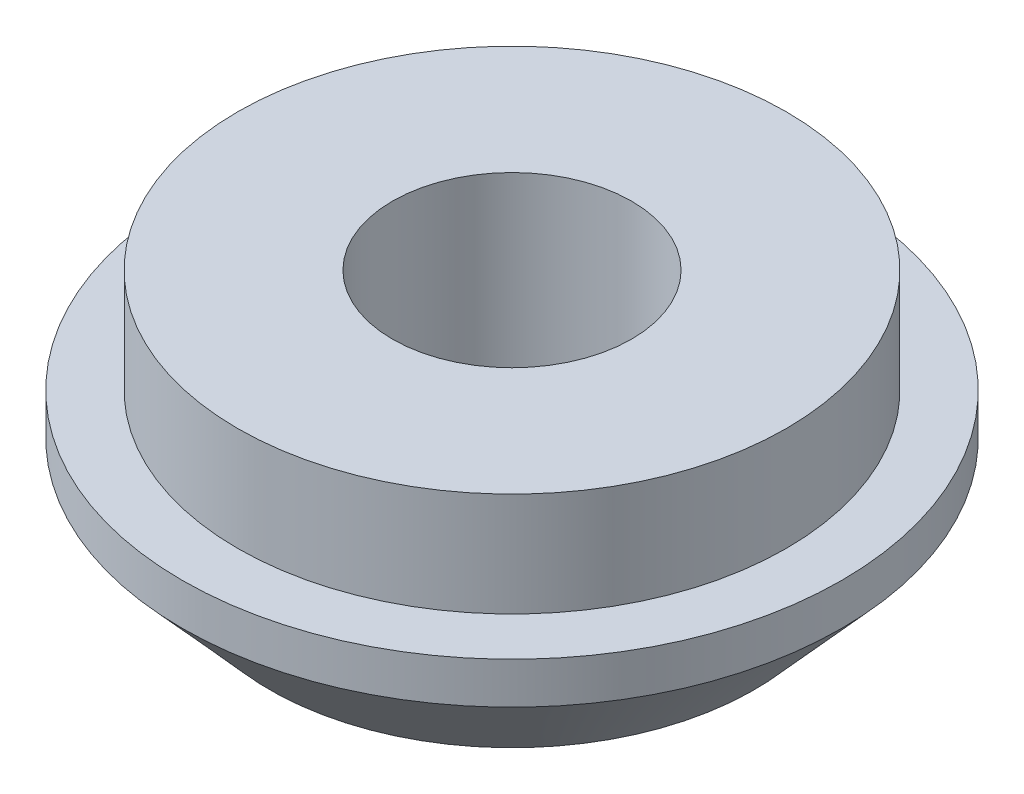
SolidWorks part; units mm, degrees
material "Plain Carbon Steel"
ref_plane "Front Plane" through (0, 0, 0) normal (0, 0, 1) x (1, 0, 0)
ref_plane "Top Plane" through (0, 0, 0) normal (0, 1, 0) x (1, 0, 0)
ref_plane "Right Plane" through (0, 0, 0) normal (1, 0, 0) x (0, 0, -1)
sketch "Sketch1" plane through (0, 0, 0) normal (0, 1, 0) x (1, 0, 0)
  circle A0 centre (0, 0) radius 9.525
  dimension "D1" = 19.05
extrude "Extrude1" add sketch "Sketch1" along normal blind 7
hole_wizard "5/16-24 Tapped Hole1" positions "Sketch8" profile "Sketch7" tap size "5/16-24" standard "ANSI Inch" end condition through all
sketch "Sketch8" plane through (0, 0, 0) normal (0, -1, 0) x (-1, 0, 0)
  point P0 (0, 0)
sketch "Sketch7" plane through (0, 0, 0) normal (1, 0, 0) x (0, 0, -1)
  line L0 (0, 0) -> (0, 7)
  line L1 (0, 7) -> (3.4544, 7)
  line L2 (3.4544, 7) -> (3.4544, 0)
  line L5 (3.4544, 0) -> (0, 0)
  line L11 (0, -6.35) -> (0, 107.95) construction
  dimension "Thru Tap Drill Dia." = 6.9088
  dimension "Thru Tap Drill Depth" = 7
cosmetic thread "Hole Thread1"
sketch "Sketch3" plane through (0, 7, 0) normal (0, 1, 0) x (1, 0, 0)
  circle A0 centre (0, 0) radius 7.925
  circle A1 centre (0, 0) radius 9.525 construction
  dimension "D1" = 1.6
extrude "Extrude3" cut sketch "Sketch3" against normal blind 3 flip side to cut
sketch "Sketch5" plane through (0, 0, 0) normal (1, 0, 0) x (0, 0, -1)
  line L0 (0, 45.7263) -> (0, -5.8121) construction
sketch "Sketch6" plane through (0, 0, 0) normal (0, 0, 1) x (1, 0, 0)
  line L0 (0, 0) -> (0, 9.5167) construction
  line L1 (-9.525, 2.8) -> (-7, 0)
  line L2 (-9.525, 4) -> (-9.525, 0) construction
  line L3 (-9.525, 0) -> (9.525, 0) construction
  line L4 (-7, 0) -> (-7, -3.8114)
  line L5 (-7, -3.8114) -> (-11.8585, -3.8114)
  line L6 (-11.8585, -3.8114) -> (-11.8585, 2.8)
  line L7 (-11.8585, 2.8) -> (-9.525, 2.8)
  line L8 (9.525, 4) -> (-9.525, 4) construction
  dimension "D1" = 1.2
  dimension "D2" = 14
revolve "Cut-Revolve1" cut sketch "Sketch6" angle 360 about L0
